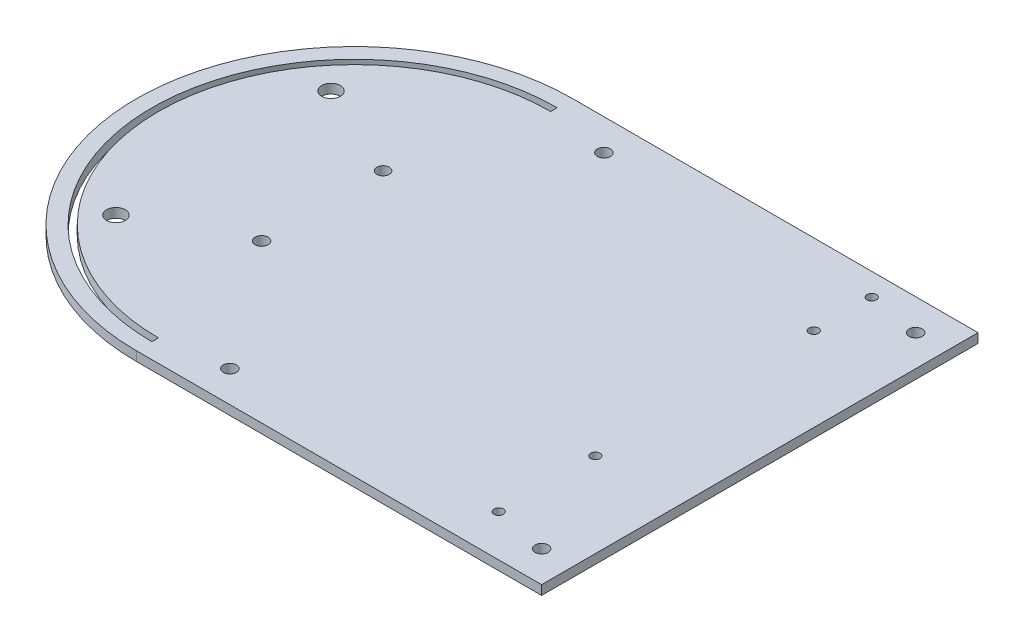
SolidWorks part; units mm, degrees
ref_plane "Front Plane" through (0, 0, 0) normal (0, 0, 1) x (1, 0, 0)
ref_plane "Top Plane" through (0, 0, 0) normal (0, 1, 0) x (1, 0, 0)
ref_plane "Right Plane" through (0, 0, 0) normal (1, 0, 0) x (0, 0, -1)
sketch "Sketch1" plane through (0, 0, 0) normal (0, 1, 0) x (1, 0, 0)
  line L0 (55, 64.1271) -> (55, -149.499) construction
  line L1 (65, -70) -> (-65, -70)
  line L2 (65, -70) -> (65, 70)
  line L3 (65, 70) -> (-65, 70)
  line L5 (65, -70) -> (-65, 70) construction
  line L6 (65, 70) -> (-65, -70) construction
  line L7 (-1000, 0) -> (49000, 0) construction
  line L14 (-65, 65) -> (-65, 62.9)
  line L15 (-65, -62.9) -> (-65, -65)
  arc A0 (-65, -70) -> (-65, 70) centre (-65, 0) cw
  arc A1 (-65, -65) -> (-65, 65) centre (-65, 0) cw
  arc A2 (-65, -62.9) -> (-65, 62.9) centre (-65, 0) cw
  circle A3 centre (-45, -60) radius 2.1
  circle A4 centre (-45, 60) radius 2.1
  circle A5 centre (55, -60) radius 2.1
  circle A6 centre (55, 60) radius 2.1
  circle A9 centre (37.842, -25.6) radius 1.5
  circle A10 centre (37.842, -56.6) radius 1.5
  circle A11 centre (38.0993, 44.2) radius 1.5
  circle A12 centre (38.0993, 62.8) radius 1.5
  circle A13 centre (-75.4006, -19.4261) radius 2.1
  circle A14 centre (-75.3997, 19.5526) radius 2
  circle A15 centre (-105.9357, 33.3886) radius 3
  circle A16 centre (-105.9357, -35.6114) radius 3
  point P0 (0, 0)
  point P14 (-130, 0)
  point P15 (-135, 0)
  point P19 (-127.9, 0)
  dimension "D9" = 7.1
  dimension "D1" = 140
  dimension "D2" = 130
  dimension "D3" = 10
  dimension "D4" = 5
  dimension "D5" = 5
  dimension "D6" = 5
  dimension "D7" = 7.1
  dimension "D8" = 7.1
extrude "Boss-Extrude1" add sketch "Sketch1" along normal blind 3
